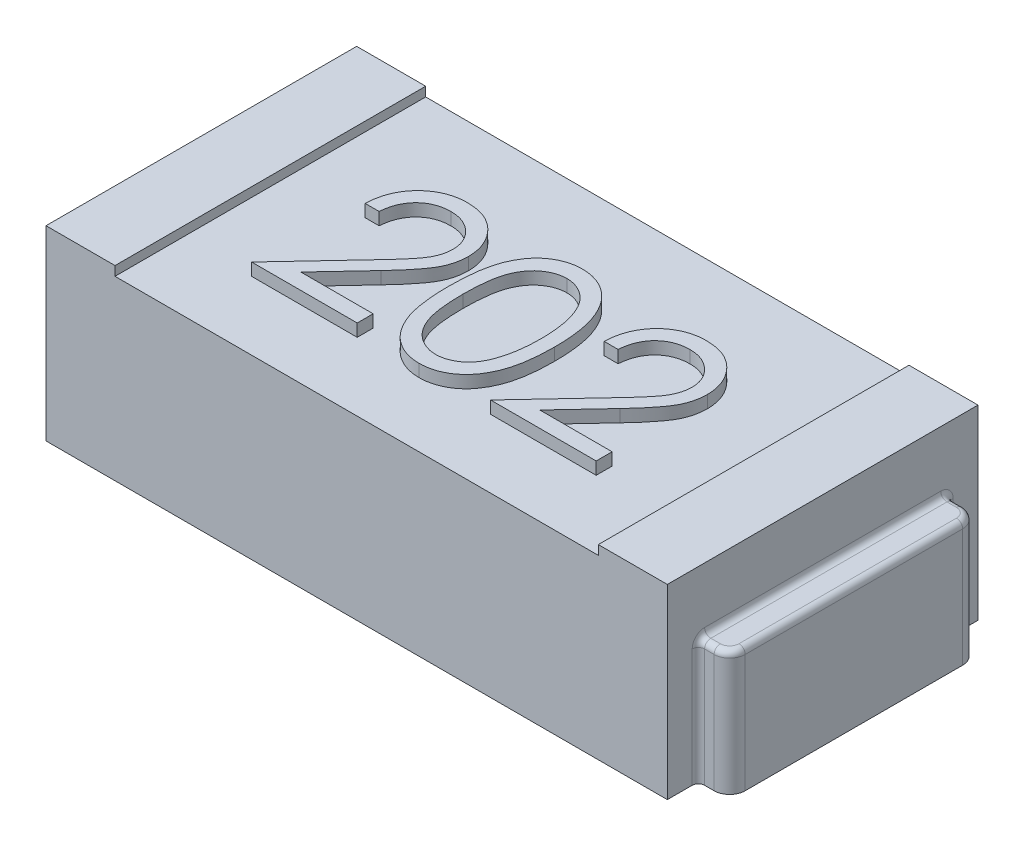
SolidWorks part; units mm, degrees
ref_plane "Plan de face" through (0, 0, 0) normal (0, 0, 1) x (1, 0, 0)
ref_plane "Plan de dessus" through (0, 0, 0) normal (0, 1, 0) x (1, 0, 0)
ref_plane "Plan de droite" through (0, 0, 0) normal (1, 0, 0) x (0, 0, -1)
sketch "Esquisse1" plane through (0, 0, 0) normal (0, 1, 0) x (1, 0, 0)
  line L1 (1, -0.5) -> (-1, -0.5)
  line L2 (1, -0.5) -> (1, 0.5)
  line L3 (1, 0.5) -> (-1, 0.5)
  line L4 (-1, -0.5) -> (-1, 0.5)
  line L5 (1, -0.5) -> (-1, 0.5) construction
  line L6 (1, 0.5) -> (-1, -0.5) construction
  point P0 (0, 0)
  dimension "D1" = 2
  dimension "D2" = 1
extrude "Boss.-Extru.1" add sketch "Esquisse1" along normal blind 0.6
sketch "Esquisse2" plane through (0, 0.6, 0) normal (0, 1, 0) x (1, 0, 0)
  line L0 (1, 0.5) -> (-1, 0.5) construction
  line L1 (0.7778, -0.5) -> (-0.7778, -0.5)
  line L2 (0.7778, -0.5) -> (0.7778, 0.5)
  line L3 (0.7778, 0.5) -> (-0.7778, 0.5)
  line L4 (-0.7778, -0.5) -> (-0.7778, 0.5)
  line L5 (0.7778, -0.5) -> (-0.7778, 0.5) construction
  line L6 (0.7778, 0.5) -> (-0.7778, -0.5) construction
  point P0 (0, 0)
extrude "Enlèv. mat.-Extru.1" cut sketch "Esquisse2" against normal blind 0.03
sketch "Esquisse3" plane through (0, 0, 0) normal (0, 1, 0) x (1, 0, 0)
  line L1 (1, 0.4) -> (1.0506, 0.4)
  line L2 (1, 0.4) -> (1, -0.4)
  line L3 (1, -0.4) -> (1.0506, -0.4)
  line L4 (1.1006, 0.35) -> (1.1006, -0.35)
  line L8 (1, -0.5) -> (1, 0.5) construction
  arc A0 (1.0506, -0.4) -> (1.1006, -0.35) centre (1.0506, -0.35) ccw
  arc A1 (1.0506, 0.4) -> (1.1006, 0.35) centre (1.0506, 0.35) cw
  dimension "D1" = 0.05
  dimension "D2" = 0.8
  dimension "D3" = 0.1006
extrude "Boss.-Extru.2" add sketch "Esquisse3" along normal blind 0.4
fillet "Congé1" radius 0.02 8 edges at (1, 0.2, -0.4) (1, 0.2, 0.4) (1.0253, 0.4, -0.4) (1.0859, 0.4, -0.3854) (1.1006, 0.4, 0) (1.0859, 0.4, 0.3854) (1.0253, 0.4, 0.4) (1, 0.4, 0)
mirror "Symétrie2" about plane through (0, 0, 0) normal (1, 0, 0) of "Congé1", "Boss.-Extru.2"
sketch "Esquisse4" plane through (0, 0.57, 0) normal (0, 1, 0) x (1, 0, 0)
  line L0 (0.7576, -0.2803) -> (-0.7576, -0.2803) construction
  text T0 "202\r\n\r\n" font "Century Gothic" height 0.5
  point P3 (0, -0.2803)
extrude "Boss.-Extru.3" add sketch "Esquisse4" along normal blind 0.04
